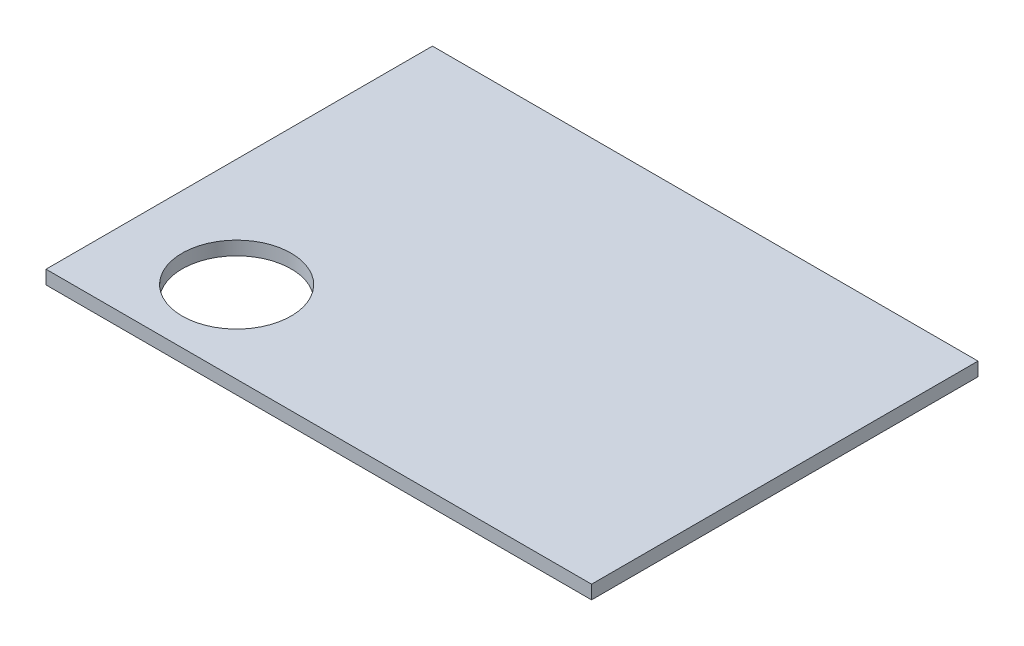
SolidWorks part; units mm, degrees
ref_plane "Front Plane" through (0, 0, 0) normal (0, 0, 1) x (1, 0, 0)
ref_plane "Top Plane" through (0, 0, 0) normal (0, 1, 0) x (1, 0, 0)
ref_plane "Right Plane" through (0, 0, 0) normal (1, 0, 0) x (0, 0, -1)
sketch "Sketch1" plane through (0, 0, 0) normal (0, 1, 0) x (1, 0, 0)
  line L1 (60, -42.5) -> (-60, -42.5)
  line L2 (60, -42.5) -> (60, 42.5)
  line L3 (60, 42.5) -> (-60, 42.5)
  line L4 (-60, -42.5) -> (-60, 42.5)
  line L5 (60, -42.5) -> (-60, 42.5) construction
  line L6 (60, 42.5) -> (-60, -42.5) construction
  point P0 (0, 0)
  dimension "D1" = 120
  dimension "D2" = 85
extrude "Boss-Extrude1" add sketch "Sketch1" along normal blind 3
sketch "Sketch2" plane through (0, 3, 0) normal (0, 1, 0) x (1, 0, 0)
  line L0 (-60, 42.5) -> (-60, -42.5) construction
  line L3 (-60, -42.5) -> (60, -42.5) construction
  circle A0 centre (-36.1, -24.47) radius 11.99
  point P2 (0, 0)
  point P7 (-36.9271, -42.5)
  point P8 (-35.1587, -42.5)
  dimension "D1" = 23.98
  dimension "D2" = 23.9
  dimension "D3" = 18.03
extrude "Cut-Extrude1" cut sketch "Sketch2" against normal blind 3
